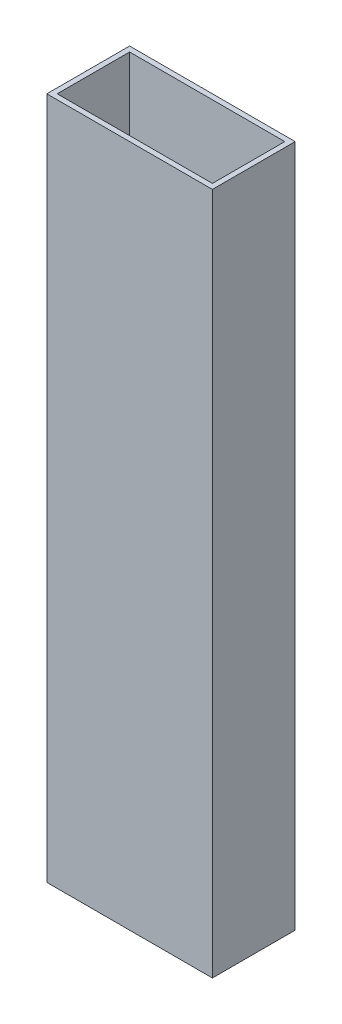
SolidWorks part; units mm, degrees
ref_plane "Front Plane" through (0, 0, 0) normal (0, 0, 1) x (1, 0, 0)
ref_plane "Top Plane" through (0, 0, 0) normal (0, 1, 0) x (1, 0, 0)
ref_plane "Right Plane" through (0, 0, 0) normal (1, 0, 0) x (0, 0, -1)
sketch "Sketch1" plane through (0, 0, 0) normal (0, 1, 0) x (1, 0, 0)
  line L1 (-30.1782, 19.029) -> (20.6218, 19.029)
  line L2 (-30.1782, 19.029) -> (-30.1782, -6.371)
  line L3 (-30.1782, -6.371) -> (20.6218, -6.371)
  line L4 (20.6218, 19.029) -> (20.6218, -6.371)
  line L5 (-28.5907, 17.4415) -> (19.0343, 17.4415)
  line L6 (-28.5907, 17.4415) -> (-28.5907, -4.7835)
  line L7 (-28.5907, -4.7835) -> (19.0343, -4.7835)
  line L8 (19.0343, 17.4415) -> (19.0343, -4.7835)
  dimension "D1" = 50.8
  dimension "D2" = 25.4
  dimension "D3" = 1.5875
  dimension "D4" = 1.5875
  dimension "D5" = 1.5875
  dimension "D6" = 1.5875
extrude "Boss-Extrude1" add sketch "Sketch1" along normal blind 209.55
